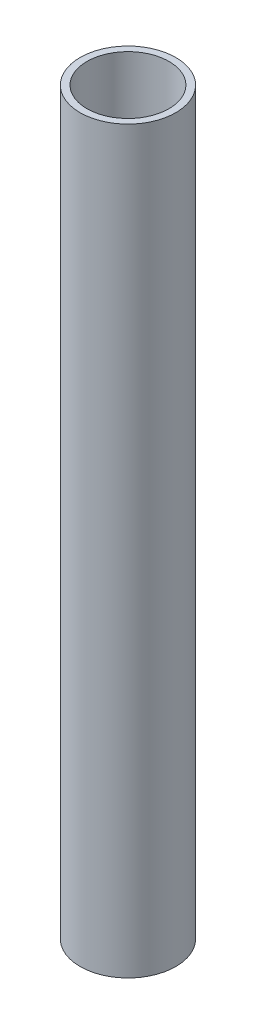
SolidWorks part; units mm, degrees
ref_plane "Front Plane" through (0, 0, 0) normal (0, 0, 1) x (1, 0, 0)
ref_plane "Top Plane" through (0, 0, 0) normal (0, 1, 0) x (1, 0, 0)
ref_plane "Right Plane" through (0, 0, 0) normal (1, 0, 0) x (0, 0, -1)
sketch "Sketch1" plane through (0, 0, 0) normal (0, 1, 0) x (1, 0, 0)
  circle A0 centre (0, 0) radius 13.975
  circle A1 centre (0, 0) radius 11.975
  dimension "D1" = 27.95
  dimension "D2" = 2
extrude "Boss-Extrude1" add sketch "Sketch1" along normal blind 216 contours A1 | A0
ref_point "Point1"
equation "\"D1@Boss-Extrude1\"=4+7+205"
